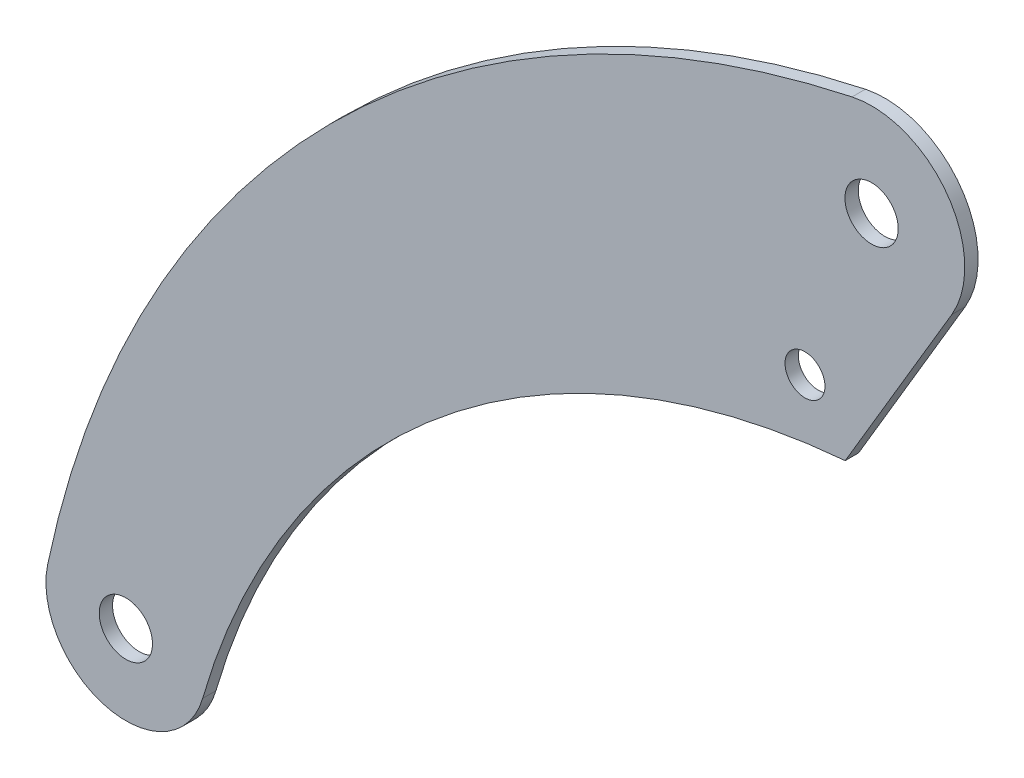
SolidWorks part; units mm, degrees
ref_plane "Front Plane" through (0, 0, 0) normal (0, 0, 1) x (1, 0, 0)
ref_plane "Top Plane" through (0, 0, 0) normal (0, 1, 0) x (1, 0, 0)
ref_plane "Right Plane" through (0, 0, 0) normal (1, 0, 0) x (0, 0, -1)
sketch "Sketch1" plane through (0, 0, 0) normal (0, 0, 1) x (1, 0, 0)
  line L0 (60.2204, -35.6862) -> (-19.7796, -170.6862)
  circle A0 centre (0, 0) radius 20
  circle A1 centre (-50, -130) radius 15
  circle A2 centre (-560, -550) radius 20
  arc A3 (-618.7157, -537.6524) -> (-502.3419, -566.5995) centre (-560, -550) ccw
  arc A4 (-14.6346, 68.4531) -> (60.2204, -35.6862) centre (0, 0) cw
  arc A5 (-19.7796, -170.6862) -> (-502.3419, -566.5995) centre (26.1907, -718.7616) ccw
  arc A6 (-618.7157, -537.6524) -> (-14.6346, 68.4531) centre (149.4818, -699.1997) cw
  dimension "D1" = 40
  dimension "D2" = 30
  dimension "D3" = 40
  dimension "D8" = 60
  dimension "D9" = 70
  dimension "D12" = 550
  dimension "D13" = 785
  dimension "D4" = 50
  dimension "D5" = 130
  dimension "D6" = 560
  dimension "D7" = 550
  dimension "D10" = 135
  dimension "D11" = 80
extrude "Boss-Extrude1" add sketch "Sketch1" along normal mid plane 10
